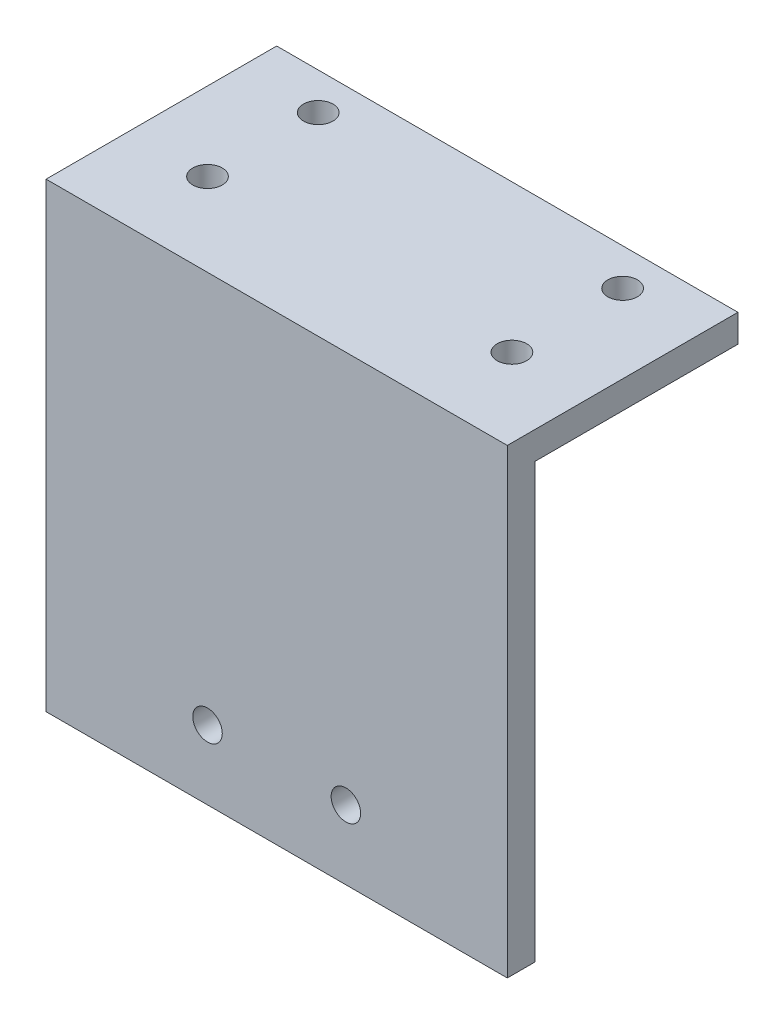
SolidWorks part; units mm, degrees
ref_plane "正面" through (0, 0, 0) normal (0, 0, 1) x (1, 0, 0)
ref_plane "平面" through (0, 0, 0) normal (0, 1, 0) x (1, 0, 0)
ref_plane "右側面" through (0, 0, 0) normal (1, 0, 0) x (0, 0, -1)
sketch "ｽｹｯﾁ1" plane through (0, 0, 0) normal (1, 0, 0) x (0, 0, -1)
  line L0 (0, 50) -> (25, 50)
  line L1 (25, 50) -> (25, 47)
  line L2 (25, 47) -> (3, 47)
  line L3 (3, 47) -> (3, 0)
  line L4 (3, 0) -> (0, 0)
  line L5 (0, 0) -> (0, 50)
  dimension "D1" = 25
  dimension "D2" = 50
  dimension "D3" = 3
  dimension "D4" = 3
extrude "ﾎﾞｽ - 押し出し1" add sketch "ｽｹｯﾁ1" along normal blind 50
sketch "ｽｹｯﾁ2" plane through (0, 47, 0) normal (0, -1, 0) x (1, 0, 0)
  line L0 (0, -9) -> (50, -9) construction
  line L1 (8.5, -3) -> (8.5, -25) construction
  line L2 (41.5, -3) -> (41.5, -25) construction
  line L3 (0, -21) -> (50, -21) construction
  line L5 (50, -3) -> (0, -3) construction
  line L6 (0, -3) -> (0, -25) construction
  line L7 (50, -3) -> (50, -25) construction
  line L8 (50, -25) -> (0, -25) construction
  circle A0 centre (8.5, -9) radius 1.6
  circle A1 centre (8.5, -21) radius 1.6
  circle A2 centre (41.5, -9) radius 1.6
  circle A3 centre (41.5, -21) radius 1.6
  dimension "D1" = 6
  dimension "D5" = 3.2
  dimension "D2" = 18
  dimension "D3" = 8.5
  dimension "D4" = 41.5
extrude "ｶｯﾄ - 押し出し1" cut sketch "ｽｹｯﾁ2" against normal through all
sketch "ｽｹｯﾁ3" plane through (0, 0, 0) normal (0, 0, 1) x (1, 0, 0)
  line L0 (50, 50) -> (0, 50) construction
  line L7 (0, 50) -> (0, 0) construction
  line L9 (0, 12) -> (50, 12) construction
  line L10 (0, 12) -> (0, 3) construction
  line L11 (0, 3) -> (50, 3) construction
  line L12 (50, 12) -> (50, 3) construction
  line L13 (0, 12) -> (50, 3) construction
  line L14 (0, 3) -> (50, 12) construction
  line L15 (0, 7.5) -> (50, 7.5) construction
  circle A2 centre (17.5, 7.5) radius 1.6
  circle A3 centre (32.5, 7.5) radius 1.6
  point P9 (25, 7.5)
  dimension "D7" = 3.2
  dimension "D8" = 3.2
  dimension "D3" = 9
  dimension "D4" = 38
  dimension "D11" = 7.5
  dimension "D12" = 7.5
extrude "ｶｯﾄ - 押し出し2" cut sketch "ｽｹｯﾁ3" against normal through all
